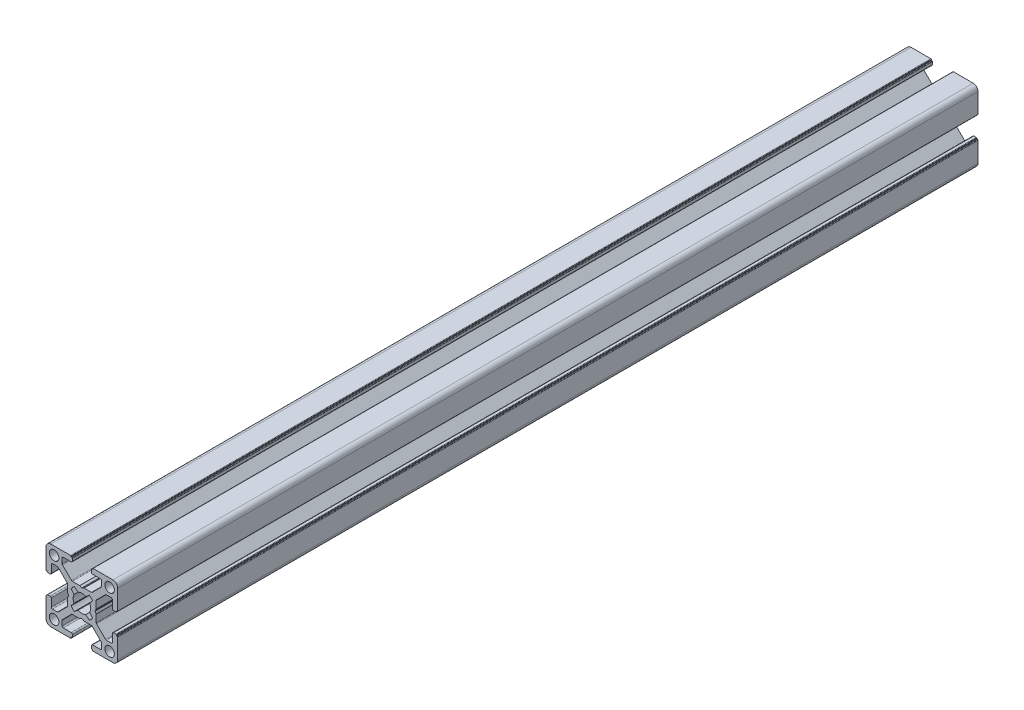
SolidWorks part; units mm, degrees
ref_plane "Alzado" through (0, 0, 0) normal (0, 0, 1) x (1, 0, 0)
ref_plane "Planta" through (0, 0, 0) normal (0, 1, 0) x (1, 0, 0)
ref_plane "Vista lateral" through (0, 0, 0) normal (1, 0, 0) x (0, 0, -1)
ref_plane "Plano1" through (0, 0, 1000) normal (0, 0, 1) x (1, 0, 0)
sketch "Croquis1" plane through (0, 0, 1000) normal (0, 0, 1) x (1, 0, 0)
  line L16 (-7.8359, -10.4816) -> (-6.3001, -11.7194)
  line L17 (-3.0999, -11.7194) -> (-1.5641, -10.4816)
  line L18 (-0.1947, -11.8453) -> (-1.4194, -13.3999)
  line L19 (-1.4194, -16.6001) -> (-0.1947, -18.1547)
  line L20 (-1.5641, -19.5184) -> (-3.0999, -18.2806)
  line L21 (-6.3001, -18.2806) -> (-7.8359, -19.5184)
  line L22 (-9.2053, -18.1547) -> (-7.9806, -16.6001)
  line L23 (-7.9806, -13.3999) -> (-9.2053, -11.8453)
  line L24 (9.8, -10.5) -> (10.1, -10.5)
  line L25 (10.3, -10.3) -> (10.3, -2)
  line L26 (8.3, 0) -> (0, 0)
  line L27 (-0.2, -0.2) -> (-0.2, -0.5)
  line L28 (-0.2, -0.5) -> (-0.5, -0.5)
  line L29 (-0.7, -0.7) -> (-0.7, -1.7)
  line L30 (-0.2, -2.2) -> (3.05, -2.2)
  line L31 (3.55, -2.7) -> (3.55, -4.7431)
  line L32 (3.4037, -5.0964) -> (-0.3491, -8.8534)
  line L33 (-0.7028, -9) -> (-3.7468, -9)
  line L34 (-3.8462, -9.0264) -> (-4.6006, -9.4583)
  line L35 (-4.7994, -9.4583) -> (-5.5538, -9.0264)
  line L36 (-5.6532, -9) -> (-8.6972, -9)
  line L37 (-9.0509, -8.8534) -> (-12.8037, -5.0964)
  line L38 (-12.95, -4.7431) -> (-12.95, -2.7)
  line L39 (-12.45, -2.2) -> (-9.2, -2.2)
  line L40 (-8.7, -1.7) -> (-8.7, -0.7)
  line L41 (-8.9, -0.5) -> (-9.2, -0.5)
  line L42 (-9.2, -0.5) -> (-9.2, -0.2)
  line L43 (-9.4, 0) -> (-17.7, 0)
  line L44 (-19.7, -2) -> (-19.7, -10.3)
  line L45 (-19.5, -10.5) -> (-19.2, -10.5)
  line L46 (-19.2, -10.5) -> (-19.2, -10.8)
  line L47 (-19, -11) -> (-18, -11)
  line L48 (-17.5, -10.5) -> (-17.5, -7.25)
  line L49 (-17, -6.75) -> (-14.9569, -6.75)
  line L50 (-14.6036, -6.8963) -> (-10.8466, -10.6491)
  line L51 (-10.7, -11.0028) -> (-10.7, -14.0468)
  line L52 (-10.6736, -14.1462) -> (-10.2417, -14.9006)
  line L53 (-10.2417, -15.0994) -> (-10.6736, -15.8538)
  line L54 (-10.7, -15.9532) -> (-10.7, -18.9972)
  line L55 (-10.8466, -19.3509) -> (-14.6036, -23.1037)
  line L56 (-14.9569, -23.25) -> (-17, -23.25)
  line L57 (-17.5, -22.75) -> (-17.5, -19.5)
  line L58 (-18, -19) -> (-19, -19)
  line L59 (-19.2, -19.2) -> (-19.2, -19.5)
  line L60 (-19.2, -19.5) -> (-19.5, -19.5)
  line L61 (-19.7, -19.7) -> (-19.7, -28)
  line L62 (-17.7, -30) -> (-9.4, -30)
  line L63 (-9.2, -29.8) -> (-9.2, -29.5)
  line L64 (-9.2, -29.5) -> (-8.9, -29.5)
  line L65 (-8.7, -29.3) -> (-8.7, -28.3)
  line L66 (-9.2, -27.8) -> (-12.45, -27.8)
  line L67 (-12.95, -27.3) -> (-12.95, -25.2569)
  line L68 (-12.8037, -24.9036) -> (-9.0509, -21.1466)
  line L69 (-8.6972, -21) -> (-5.6532, -21)
  line L70 (-5.5538, -20.9736) -> (-4.7994, -20.5417)
  line L71 (-4.6006, -20.5417) -> (-3.8462, -20.9736)
  line L72 (-3.7468, -21) -> (-0.7028, -21)
  line L73 (-0.3491, -21.1466) -> (3.4037, -24.9036)
  line L74 (3.55, -25.2569) -> (3.55, -27.3)
  line L75 (3.05, -27.8) -> (-0.2, -27.8)
  line L76 (-0.7, -28.3) -> (-0.7, -29.3)
  line L77 (-0.5, -29.5) -> (-0.2, -29.5)
  line L78 (-0.2, -29.5) -> (-0.2, -29.8)
  line L79 (0, -30) -> (8.3, -30)
  line L80 (10.3, -28) -> (10.3, -19.7)
  line L81 (10.1, -19.5) -> (9.8, -19.5)
  line L82 (9.8, -19.5) -> (9.8, -19.2)
  line L83 (9.6, -19) -> (8.6, -19)
  line L84 (8.1, -19.5) -> (8.1, -22.75)
  line L85 (7.6, -23.25) -> (5.5569, -23.25)
  line L86 (5.2036, -23.1037) -> (1.4466, -19.3509)
  line L87 (1.3, -18.9972) -> (1.3, -15.9532)
  line L88 (1.2736, -15.8538) -> (0.8417, -15.0994)
  line L89 (0.8417, -14.9006) -> (1.2736, -14.1462)
  line L90 (1.3, -14.0468) -> (1.3, -11.0028)
  line L91 (1.4466, -10.6491) -> (5.2036, -6.8963)
  line L92 (5.5569, -6.75) -> (7.6, -6.75)
  line L93 (8.1, -7.25) -> (8.1, -10.5)
  line L94 (8.6, -11) -> (9.6, -11)
  line L95 (9.8, -10.8) -> (9.8, -10.5)
  line L96 (8, -2.3) -> (5.8, -4.5) construction
  line L97 (-15.2, -2.3) -> (-17.4, -4.5) construction
  line L98 (-4.7, -15) -> (6.9, -15) construction
  arc A16 (-9.2053, -11.8453) -> (-7.8359, -10.4816) centre (-4.7, -15) cw
  arc A17 (-6.3001, -11.7194) -> (-3.0999, -11.7194) centre (-4.7, -15) cw
  arc A18 (-1.5641, -10.4816) -> (-0.1947, -11.8453) centre (-4.7, -15) cw
  arc A19 (-1.4194, -13.3999) -> (-1.4194, -16.6001) centre (-4.7, -15) cw
  arc A20 (-0.1947, -18.1547) -> (-1.5641, -19.5184) centre (-4.7, -15) cw
  arc A21 (-3.0999, -18.2806) -> (-6.3001, -18.2806) centre (-4.7, -15) cw
  arc A22 (-7.8359, -19.5184) -> (-9.2053, -18.1547) centre (-4.7, -15) cw
  arc A23 (-7.9806, -16.6001) -> (-7.9806, -13.3999) centre (-4.7, -15) cw
  arc A24 (10.1, -10.5) -> (10.3, -10.3) centre (10.1, -10.3) ccw
  arc A25 (10.3, -2) -> (8.3, 0) centre (8.3, -2) ccw
  arc A26 (0, 0) -> (-0.2, -0.2) centre (0, -0.2) ccw
  arc A27 (-0.5, -0.5) -> (-0.7, -0.7) centre (-0.5, -0.7) ccw
  arc A28 (-0.7, -1.7) -> (-0.2, -2.2) centre (-0.2, -1.7) ccw
  arc A29 (3.05, -2.2) -> (3.55, -2.7) centre (3.05, -2.7) cw
  arc A30 (3.55, -4.7431) -> (3.4037, -5.0964) centre (3.05, -4.7431) cw
  arc A31 (-0.3491, -8.8534) -> (-0.7028, -9) centre (-0.7028, -8.5) cw
  arc A32 (-3.7468, -9) -> (-3.8462, -9.0264) centre (-3.7468, -9.2) ccw
  arc A33 (-4.6006, -9.4583) -> (-4.7994, -9.4583) centre (-4.7, -9.2847) cw
  arc A34 (-5.5538, -9.0264) -> (-5.6532, -9) centre (-5.6532, -9.2) ccw
  arc A35 (-8.6972, -9) -> (-9.0509, -8.8534) centre (-8.6972, -8.5) cw
  arc A36 (-12.8037, -5.0964) -> (-12.95, -4.7431) centre (-12.45, -4.7431) cw
  arc A37 (-12.95, -2.7) -> (-12.45, -2.2) centre (-12.45, -2.7) cw
  arc A38 (-9.2, -2.2) -> (-8.7, -1.7) centre (-9.2, -1.7) ccw
  arc A39 (-8.7, -0.7) -> (-8.9, -0.5) centre (-8.9, -0.7) ccw
  arc A40 (-9.2, -0.2) -> (-9.4, 0) centre (-9.4, -0.2) ccw
  arc A41 (-17.7, 0) -> (-19.7, -2) centre (-17.7, -2) ccw
  arc A42 (-19.7, -10.3) -> (-19.5, -10.5) centre (-19.5, -10.3) ccw
  arc A43 (-19.2, -10.8) -> (-19, -11) centre (-19, -10.8) ccw
  arc A44 (-18, -11) -> (-17.5, -10.5) centre (-18, -10.5) ccw
  arc A45 (-17.5, -7.25) -> (-17, -6.75) centre (-17, -7.25) cw
  arc A46 (-14.9569, -6.75) -> (-14.6036, -6.8963) centre (-14.9569, -7.25) cw
  arc A47 (-10.8466, -10.6491) -> (-10.7, -11.0028) centre (-11.2, -11.0028) cw
  arc A48 (-10.7, -14.0468) -> (-10.6736, -14.1462) centre (-10.5, -14.0468) ccw
  arc A49 (-10.2417, -14.9006) -> (-10.2417, -15.0994) centre (-10.4153, -15) cw
  arc A50 (-10.6736, -15.8538) -> (-10.7, -15.9532) centre (-10.5, -15.9532) ccw
  arc A51 (-10.7, -18.9972) -> (-10.8466, -19.3509) centre (-11.2, -18.9972) cw
  arc A52 (-14.6036, -23.1037) -> (-14.9569, -23.25) centre (-14.9569, -22.75) cw
  arc A53 (-17, -23.25) -> (-17.5, -22.75) centre (-17, -22.75) cw
  arc A54 (-17.5, -19.5) -> (-18, -19) centre (-18, -19.5) ccw
  arc A55 (-19, -19) -> (-19.2, -19.2) centre (-19, -19.2) ccw
  arc A56 (-19.5, -19.5) -> (-19.7, -19.7) centre (-19.5, -19.7) ccw
  arc A57 (-19.7, -28) -> (-17.7, -30) centre (-17.7, -28) ccw
  arc A58 (-9.4, -30) -> (-9.2, -29.8) centre (-9.4, -29.8) ccw
  arc A59 (-8.9, -29.5) -> (-8.7, -29.3) centre (-8.9, -29.3) ccw
  arc A60 (-8.7, -28.3) -> (-9.2, -27.8) centre (-9.2, -28.3) ccw
  arc A61 (-12.45, -27.8) -> (-12.95, -27.3) centre (-12.45, -27.3) cw
  arc A62 (-12.95, -25.2569) -> (-12.8037, -24.9036) centre (-12.45, -25.2569) cw
  arc A63 (-9.0509, -21.1466) -> (-8.6972, -21) centre (-8.6972, -21.5) cw
  arc A64 (-5.6532, -21) -> (-5.5538, -20.9736) centre (-5.6532, -20.8) ccw
  arc A65 (-4.7994, -20.5417) -> (-4.6006, -20.5417) centre (-4.7, -20.7153) cw
  arc A66 (-3.8462, -20.9736) -> (-3.7468, -21) centre (-3.7468, -20.8) ccw
  arc A67 (-0.7028, -21) -> (-0.3491, -21.1466) centre (-0.7028, -21.5) cw
  arc A68 (3.4037, -24.9036) -> (3.55, -25.2569) centre (3.05, -25.2569) cw
  arc A69 (3.55, -27.3) -> (3.05, -27.8) centre (3.05, -27.3) cw
  arc A70 (-0.2, -27.8) -> (-0.7, -28.3) centre (-0.2, -28.3) ccw
  arc A71 (-0.7, -29.3) -> (-0.5, -29.5) centre (-0.5, -29.3) ccw
  arc A72 (-0.2, -29.8) -> (0, -30) centre (0, -29.8) ccw
  arc A73 (8.3, -30) -> (10.3, -28) centre (8.3, -28) ccw
  arc A74 (10.3, -19.7) -> (10.1, -19.5) centre (10.1, -19.7) ccw
  arc A75 (9.8, -19.2) -> (9.6, -19) centre (9.6, -19.2) ccw
  arc A76 (8.6, -19) -> (8.1, -19.5) centre (8.6, -19.5) ccw
  arc A77 (8.1, -22.75) -> (7.6, -23.25) centre (7.6, -22.75) cw
  arc A78 (5.5569, -23.25) -> (5.2036, -23.1037) centre (5.5569, -22.75) cw
  arc A79 (1.4466, -19.3509) -> (1.3, -18.9972) centre (1.8, -18.9972) cw
  arc A80 (1.3, -15.9532) -> (1.2736, -15.8538) centre (1.1, -15.9532) ccw
  arc A81 (0.8417, -15.0994) -> (0.8417, -14.9006) centre (1.0153, -15) cw
  arc A82 (1.2736, -14.1462) -> (1.3, -14.0468) centre (1.1, -14.0468) ccw
  arc A83 (1.3, -11.0028) -> (1.4466, -10.6491) centre (1.8, -11.0028) cw
  arc A84 (5.2036, -6.8963) -> (5.5569, -6.75) centre (5.5569, -7.25) cw
  arc A85 (7.6, -6.75) -> (8.1, -7.25) centre (7.6, -7.25) cw
  arc A86 (8.1, -10.5) -> (8.6, -11) centre (8.6, -10.5) ccw
  arc A87 (9.6, -11) -> (9.8, -10.8) centre (9.6, -10.8) ccw
  circle A88 centre (-16.3, -3.4) radius 2
  circle A89 centre (6.9, -3.4) radius 2
  circle A90 centre (-16.3, -26.6) radius 2
  circle A91 centre (6.9, -26.6) radius 2
  dimension "D3" = 4
  dimension "D1" = 30
  dimension "D2" = 30
  dimension "D4" = 23.2
  dimension "D5" = 23.2
extrude "Saliente-Extruir1" add sketch "Croquis1" against normal blind 360
